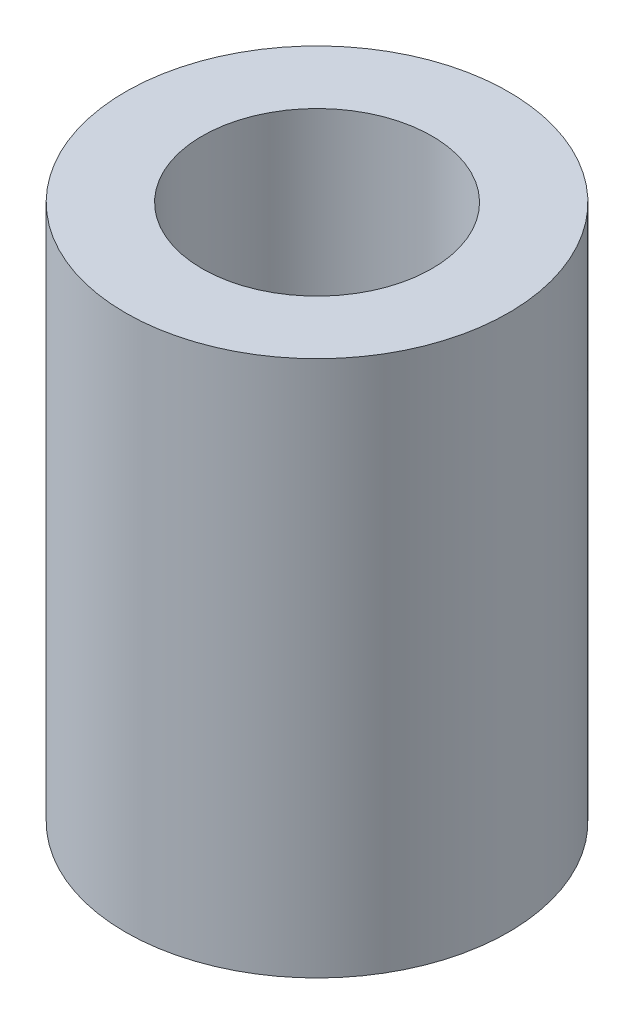
SolidWorks part; units mm, degrees
ref_plane "Front Plane" through (0, 0, 0) normal (0, 0, 1) x (1, 0, 0)
ref_plane "Top Plane" through (0, 0, 0) normal (0, 1, 0) x (1, 0, 0)
ref_plane "Right Plane" through (0, 0, 0) normal (1, 0, 0) x (0, 0, -1)
sketch "Sketch2" plane through (0, 0, 0) normal (0, 1, 0) x (1, 0, 0)
  circle A0 centre (0, 0) radius 2.5
  circle A1 centre (0, 0) radius 1.5
  dimension "D1" = 3
  dimension "D2" = 5
extrude "Boss-Extrude1" add sketch "Sketch2" along normal blind 7
